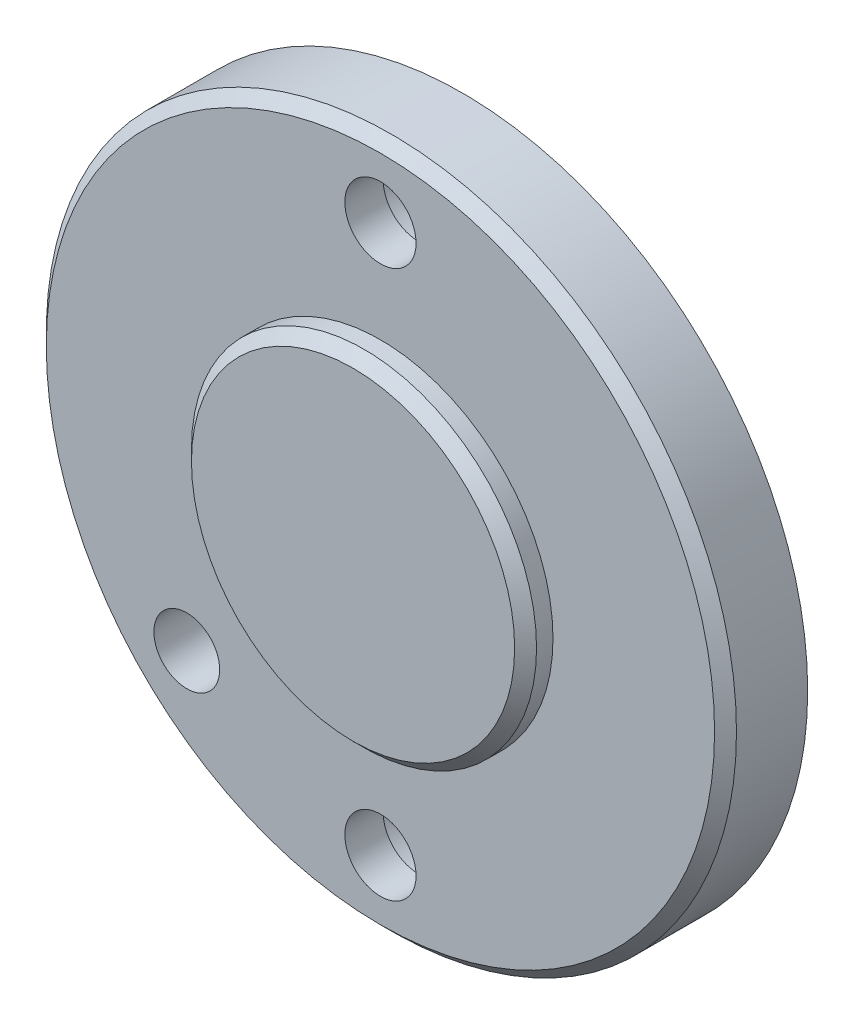
SolidWorks part; units mm, degrees
ref_plane "前视基准面" through (0, 0, 0) normal (0, 0, 1) x (1, 0, 0)
ref_plane "上视基准面" through (0, 0, 0) normal (0, 1, 0) x (1, 0, 0)
ref_plane "右视基准面" through (0, 0, 0) normal (1, 0, 0) x (0, 0, -1)
sketch "草图1" plane through (0, 0, 0) normal (0, 0, 1) x (1, 0, 0)
  circle A0 centre (0, 0) radius 31.5
extrude "凸台-拉伸1" add sketch "草图1" along normal blind 7.5
sketch "草图2" plane through (0, 0, 7.5) normal (0, 0, 1) x (1, 0, 0)
  circle A0 centre (0, 0) radius 15.75
extrude "凸台-拉伸2" add sketch "草图2" along normal blind 2.5
chamfer "倒角1" distance 1 angle 45 1 edges at (15.75, 0, 10)
chamfer "倒角2" distance 1 angle 45 1 edges at (31.5, 0, 7.5)
sketch "草图3" plane through (0, 0, 7.5) normal (0, 0, 1) x (1, 0, 0)
  line L0 (0, 0) -> (-27.6591, -27.6591) construction
  circle A0 centre (0, 25) radius 3.25
  circle A1 centre (0, 0) radius 25 construction
  circle A2 centre (0, -25) radius 3.25
  circle A3 centre (-17.6777, -17.6777) radius 3
extrude "切除-拉伸1" cut sketch "草图3" against normal blind 6.5
sketch "草图4" plane through (0, 0, 0) normal (0, 0, -1) x (-1, 0, 0)
  line L0 (0, 0) -> (0, -25) construction
  line L1 (0, 0) -> (0, 25) construction
  circle A0 centre (0, -25) radius 5.5
  circle A1 centre (0, 25) radius 5.5
extrude "切除-拉伸2" cut sketch "草图4" against normal blind 4
sketch "草图9" plane through (0, 0, 0) normal (0, 0, -1) x (-1, 0, 0)
  circle A1 centre (0, 0) radius 15.75
extrude "凸台-拉伸5" add sketch "草图9" along normal blind 5
ref_plane "基准面1" through (0, 0, -2.5) normal (0, 0, -1) x (-1, 0, 0)
sketch "草图10" plane through (0, 0, -2.5) normal (0, 0, -1) x (-1, 0, 0)
  line L0 (0, 17.3385) -> (0, -17.2813) construction
  line L1 (0, 17.3385) -> (1.475, 17.3385)
  line L2 (1.475, 17.3385) -> (1.475, -17.2813)
  line L3 (1.475, -17.2813) -> (0, -17.2813)
  line L4 (0, -17.2813) -> (0, 17.3385)
revolve "切除-旋转1" cut sketch "草图10" angle 360 about L0
sketch "草图12" plane through (0, 0, -2.5) normal (0, 0, -1) x (-1, 0, 0)
  line L0 (-17.2241, 0) -> (17.1669, 0) construction
  line L1 (-17.2241, 0) -> (-17.2241, 1.475)
  line L2 (-17.2241, 1.475) -> (17.1669, 1.475)
  line L3 (17.1669, 1.475) -> (17.1669, 0)
  line L4 (17.1669, 0) -> (-17.2241, 0)
revolve "切除-旋转2" cut sketch "草图12" angle 360 about L0
